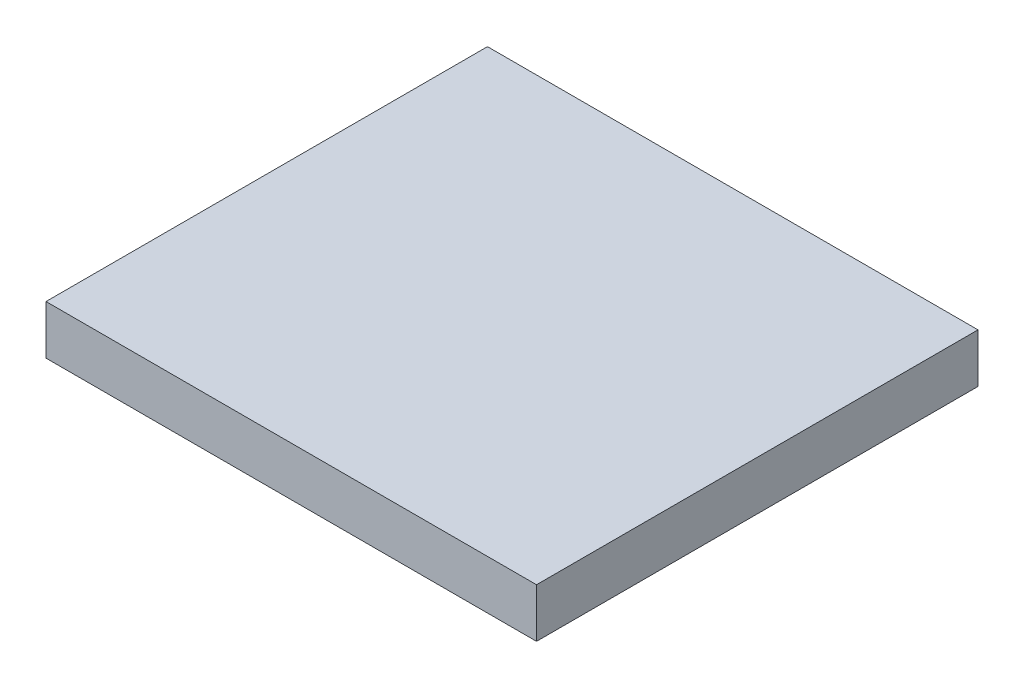
SolidWorks part; units mm, degrees
ref_plane "Plane1" through (0, 0, 0) normal (0, 0, 1) x (1, 0, 0)
ref_plane "Plane2" through (0, 0, 0) normal (0, 1, 0) x (1, 0, 0)
ref_plane "Plane3" through (0, 0, 0) normal (1, 0, 0) x (0, 0, -1)
sketch "Sketch1" plane through (0, 0, 0) normal (0, 1, 0) x (1, 0, 0)
  line L1 (0, 0) -> (100, 0)
  line L2 (0, 0) -> (0, 90)
  line L3 (0, 90) -> (100, 90)
  line L4 (100, 0) -> (100, 90)
  dimension "D1" = 100
  dimension "D2" = 90
extrude "Boss-Extrude1" add sketch "Sketch1" along normal blind 10
